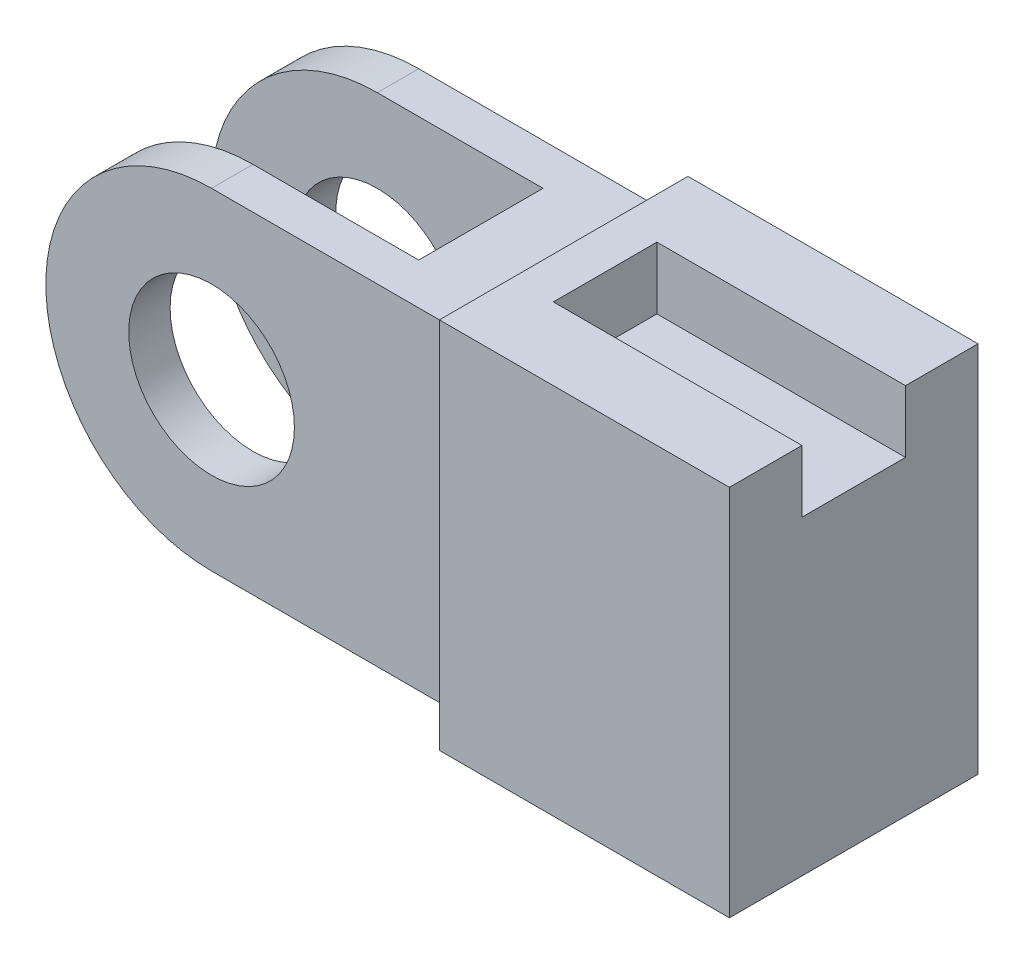
SolidWorks part; units mm, degrees
material "AISI 1020"
ref_plane "Front Plane" through (0, 0, 0) normal (0, 0, 1) x (1, 0, 0)
ref_plane "Top Plane" through (0, 0, 0) normal (0, 1, 0) x (1, 0, 0)
ref_plane "Right Plane" through (0, 0, 0) normal (1, 0, 0) x (0, 0, -1)
sketch "Sketch1" plane through (0, 0, 0) normal (0, 0, 1) x (1, 0, 0)
  line L1 (0, 0) -> (-100, 0)
  line L2 (0, 0) -> (0, 80)
  line L3 (0, 80) -> (-100, 80)
  line L4 (-100, 0) -> (-100, 80)
  arc A0 (-60, 80) -> (-60, 0) centre (-60, 40) ccw
  dimension "D1" = 100
  dimension "D2" = 80
extrude "Boss-Extrude1" add sketch "Sketch1" along normal mid plane 50 contours L3 A0 L1 L2
sketch "Sketch2" plane through (0, 0, 25) normal (0, 0, 1) x (1, 0, 0)
  circle A0 centre (-60, 40) radius 20
  arc A1 (-60, 80) -> (-60, 0) centre (-60, 40) ccw construction
  dimension "D1" = 40
extrude "Cut-Extrude1" cut sketch "Sketch2" against normal through all
sketch "Sketch3" plane through (0, 0, 0) normal (0, 0, 1) x (1, 0, 0)
  line L0 (0, 80) -> (-60, 80) construction
  line L1 (-20, 80) -> (-100, 80)
  line L2 (-20, 80) -> (-20, 0)
  line L3 (-20, 0) -> (-100, 0)
  line L4 (-100, 80) -> (-100, 0)
  line L5 (0, 0) -> (0, 80) construction
  arc A0 (-60, 80) -> (-60, 0) centre (-60, 40) ccw construction
  dimension "D1" = 20
extrude "Cut-Extrude2" cut sketch "Sketch3" against normal mid plane 30
sketch "Sketch4" plane through (0, 0, 0) normal (1, 0, 0) x (0, 0, -1)
  line L10 (30, -5) -> (30, 85)
  line L11 (30, 85) -> (-30, 85)
  line L12 (-30, 85) -> (-30, -5)
  line L13 (-30, -5) -> (30, -5)
  line L14 (30, -5) -> (30, 85)
  line L15 (30, 85) -> (-30, 85)
  line L16 (-30, 85) -> (-30, -5)
  line L17 (-30, -5) -> (30, -5)
  dimension "D1" = 5
extrude "Boss-Extrude2" add sketch "Sketch4" along normal blind 70
sketch "Sketch5" plane through (70, 0, 0) normal (1, 0, 0) x (0, 0, -1)
  line L0 (30, 85) -> (-30, 85) construction
  line L1 (12.5, 85) -> (-12.5, 85)
  line L2 (12.5, 85) -> (12.5, 70)
  line L3 (12.5, 70) -> (-12.5, 70)
  line L4 (-12.5, 85) -> (-12.5, 70)
  line L5 (12.5, 85) -> (30, 85) construction
  line L6 (-12.5, 85) -> (-30, 85) construction
  dimension "D1" = 25
  dimension "D2" = 15
extrude "Cut-Extrude3" cut sketch "Sketch5" against normal blind 60
